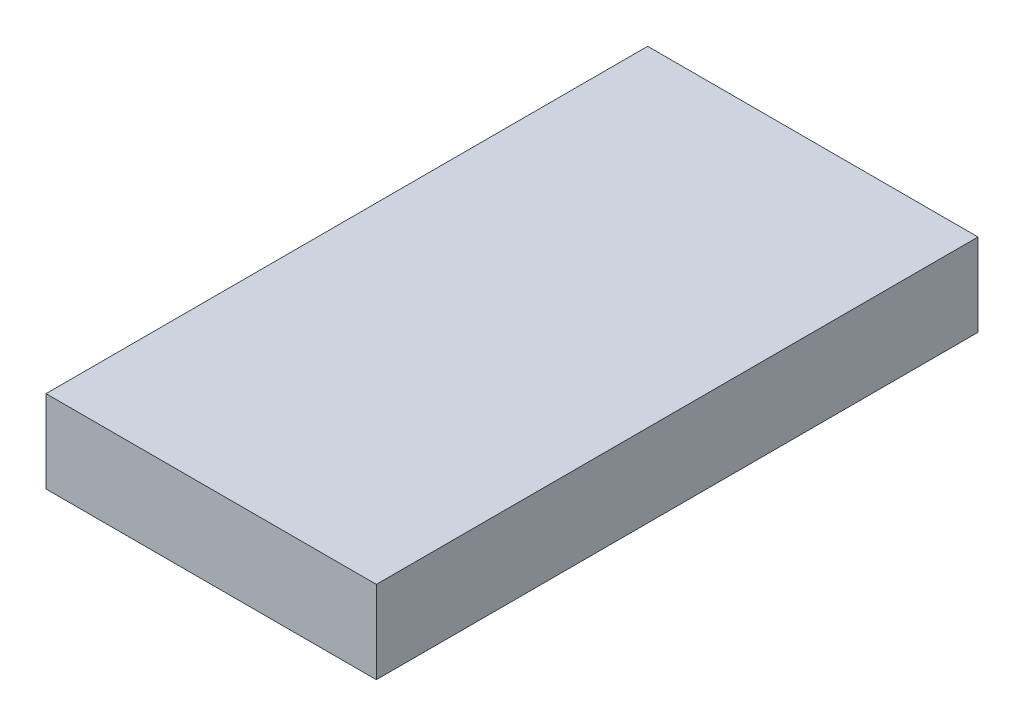
SolidWorks part; units mm, degrees
ref_plane "Front Plane" through (0, 0, 0) normal (0, 0, 1) x (1, 0, 0)
ref_plane "Top Plane" through (0, 0, 0) normal (0, 1, 0) x (1, 0, 0)
ref_plane "Right Plane" through (0, 0, 0) normal (1, 0, 0) x (0, 0, -1)
sketch "Sketch1" plane through (0, 0, 0) normal (0, 0, 1) x (1, 0, 0)
  line L1 (-56, 14) -> (56, 14)
  line L2 (-56, 14) -> (-56, -14)
  line L3 (-56, -14) -> (56, -14)
  line L4 (56, 14) -> (56, -14)
  point P7 (0, 0)
  dimension "D1" = 112
  dimension "D2" = 28
  dimension "D3" = 14
  dimension "D4" = 56
extrude "Boss-Extrude2" add sketch "Sketch1" against normal blind 204 contours L1 L4 L3 L2
sketch "Sketch2" plane through (0, 0, 0) normal (0, 0, 1) x (1, 0, 0)
  line L0 (-16.0397, 14) -> (-16.0397, 33.0819)
  line L1 (-56, 14) -> (56, 14) construction
  line L2 (-16.0397, 33.0819) -> (-20.4142, 37.4564)
  line L3 (-20.4142, 37.4564) -> (17.3156, 37.4564)
  line L4 (17.3156, 37.4564) -> (12.9411, 33.0819)
  line L5 (12.9411, 33.0819) -> (12.9411, 14)
  line L6 (12.9411, 14) -> (-16.0397, 14)
  dimension "D1" = 28.9809
